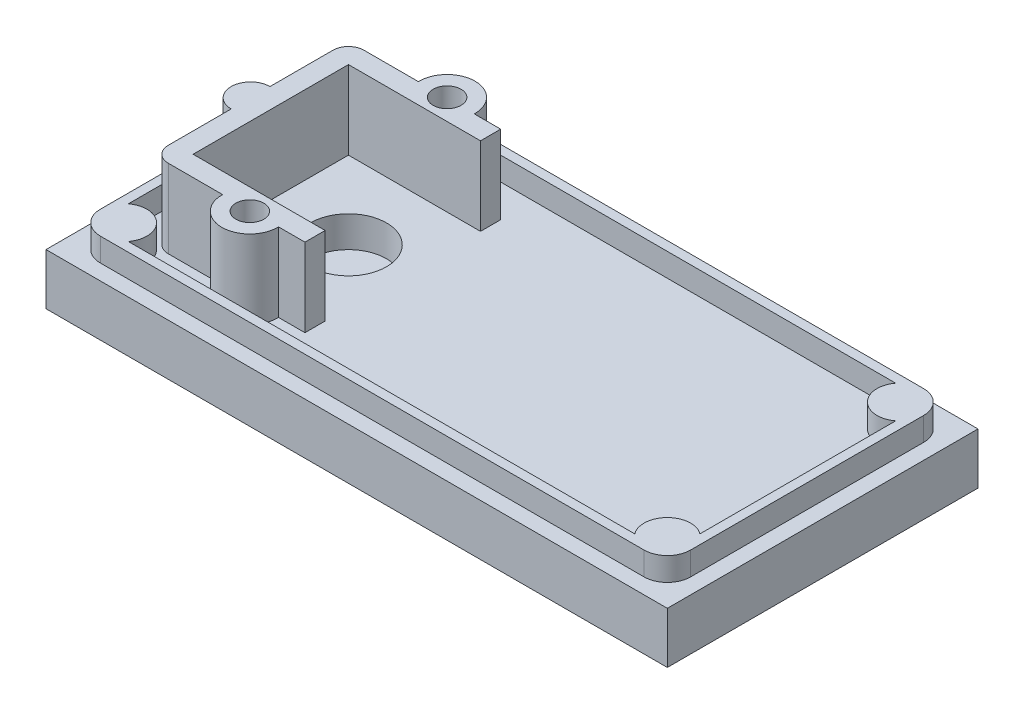
SolidWorks part; units mm, degrees
ref_plane "Front Plane" through (0, 0, 0) normal (0, 0, 1) x (1, 0, 0)
ref_plane "Top Plane" through (0, 0, 0) normal (0, 1, 0) x (1, 0, 0)
ref_plane "Right Plane" through (0, 0, 0) normal (1, 0, 0) x (0, 0, -1)
sketch "Sketch1" plane through (0, 0, 0) normal (0, 1, 0) x (1, 0, 0)
  line L0 (-20, 0) -> (73.1664, 0) construction
  line L1 (-20, -10) -> (20, -10)
  line L2 (-20, -10) -> (-20, 10)
  line L3 (-20, 10) -> (20, 10)
  line L4 (20, -10) -> (20, 10)
  line L5 (0, -10) -> (0, 29.8824) construction
  dimension "D1" = 20
  dimension "D2" = 40
extrude "Boss-Extrude1" add sketch "Sketch1" along normal blind 3.3
sketch "Sketch2" plane through (0, 3.3, 0) normal (0, 1, 0) x (1, 0, 0)
  line L8 (-19, 9) -> (-19, -9)
  line L9 (-19, -9) -> (19, -9)
  line L10 (19, -9) -> (19, 9)
  line L11 (19, 9) -> (-19, 9)
  line L12 (-19, 7.5) -> (-19, -7.5)
  line L13 (-17.5, -9) -> (17.5, -9)
  line L14 (19, -7.5) -> (19, 7.5)
  line L15 (17.5, 9) -> (-17.5, 9)
  line L20 (-18.4, 8.4) -> (-18.4, -8.4)
  line L21 (-18.4, -8.4) -> (18.4, -8.4)
  line L22 (18.4, -8.4) -> (18.4, 8.4)
  line L23 (18.4, 8.4) -> (-18.4, 8.4)
  line L24 (-18.4, 6.3) -> (-18.4, -6.3)
  line L25 (-16.3, -8.4) -> (16.3, -8.4)
  line L26 (18.4, -6.3) -> (18.4, 6.3)
  line L27 (16.3, 8.4) -> (-16.3, 8.4)
  arc A0 (-18.4, 6.3) -> (-16.3, 8.4) centre (-17.5, 7.5) ccw
  arc A1 (-17.5, 9) -> (-19, 7.5) centre (-17.5, 7.5) ccw
  arc A2 (-19, -7.5) -> (-17.5, -9) centre (-17.5, -7.5) ccw
  arc A3 (-16.3, -8.4) -> (-18.4, -6.3) centre (-17.5, -7.5) ccw
  arc A4 (17.5, -9) -> (19, -7.5) centre (17.5, -7.5) ccw
  arc A5 (18.4, -6.3) -> (16.3, -8.4) centre (17.5, -7.5) ccw
  arc A6 (16.3, 8.4) -> (18.4, 6.3) centre (17.5, 7.5) ccw
  arc A7 (19, 7.5) -> (17.5, 9) centre (17.5, 7.5) ccw
  dimension "D3" = 3
  dimension "D4" = 3
  dimension "D5" = 3
  dimension "D6" = 3
  dimension "D1" = 1
  dimension "D2" = 1.6
extrude "Boss-Extrude2" add sketch "Sketch2" along normal blind 1.5
sketch "Sketch3" plane through (0, 3.3, 0) normal (0, 1, 0) x (-1, 0, 0)
  line L0 (0, 0) -> (16.6789, 0) construction
  circle A0 centre (10.5288, 0) radius 2.45
  dimension "D1" = 4.9
extrude "Cut-Extrude1" cut sketch "Sketch3" against normal blind 2
sketch "Sketch4" plane through (0, 3.3, 0) normal (0, 1, 0) x (1, 0, 0)
  line L0 (-10.5288, 0) -> (7.452, 0) construction
  line L1 (-15.5288, -5) -> (-7.0288, -5)
  line L2 (-15.5288, -5) -> (-15.5288, 5)
  line L3 (-15.5288, 5) -> (-7.0288, 5)
  line L4 (-7.0288, -6.3) -> (-7.0288, -5)
  line L5 (-10.5288, 0) -> (-10.5288, 15.6429) construction
  line L6 (-15.8288, 6.3) -> (-12.3281, 6.3)
  line L7 (-16.8288, -5.3) -> (-16.8288, -1.25)
  line L8 (-15.8288, -6.3) -> (-12.3281, -6.3)
  line L9 (-16.8288, 6.3) -> (-5.5288, 6.3) construction
  line L10 (-16.8288, -6.3) -> (-16.8288, 6.3) construction
  line L11 (-16.8288, -6.3) -> (-5.5288, -6.3) construction
  line L12 (-7.0288, 5) -> (-7.0288, 6.3)
  line L13 (-10.5288, 0) -> (-10.5288, -12.9142) construction
  line L14 (-15.5288, -5) -> (-5.5288, -5) construction
  line L15 (-15.5288, 5) -> (-5.5288, 5) construction
  line L16 (-10.5288, 0) -> (-28.8346, 0) construction
  line L17 (-16.8288, 1.25) -> (-16.8288, 5.3)
  line L18 (-8.7295, -6.3) -> (-7.0288, -6.3)
  line L19 (-8.7295, 6.3) -> (-7.0288, 6.3)
  arc A0 (-15.8288, 6.3) -> (-16.8288, 5.3) centre (-15.8288, 5.3) ccw
  arc A1 (-16.8288, -5.3) -> (-15.8288, -6.3) centre (-15.8288, -5.3) ccw
  arc A2 (-16.8288, 1.25) -> (-16.8288, -1.25) centre (-16.8288, 0) ccw
  arc A3 (-12.3281, -6.3) -> (-8.7295, -6.3) centre (-10.5288, -6.35) ccw
  arc A4 (-8.7295, 6.3) -> (-12.3281, 6.3) centre (-10.5288, 6.35) ccw
  dimension "D4" = 1
  dimension "D6" = 2.5
  dimension "D9" = 3.6
  dimension "D10" = 3.6
  dimension "D1" = 10
  dimension "D2" = 5
  dimension "D5" = 3.5
  dimension "D7" = 1.3
  dimension "D8" = 12.7
  dimension "D3" = 1.3
extrude "Boss-Extrude3" add sketch "Sketch4" along normal blind 5.05
sketch "Sketch5" plane through (0, 8.35, 0) normal (0, 1, 0) x (-1, 0, 0)
  circle A0 centre (10.5288, 6.35) radius 0.9
  circle A1 centre (10.5288, -6.35) radius 0.9
  dimension "D1" = 1.8
  dimension "D2" = 1.8
extrude "Cut-Extrude2" cut sketch "Sketch5" against normal blind 4
